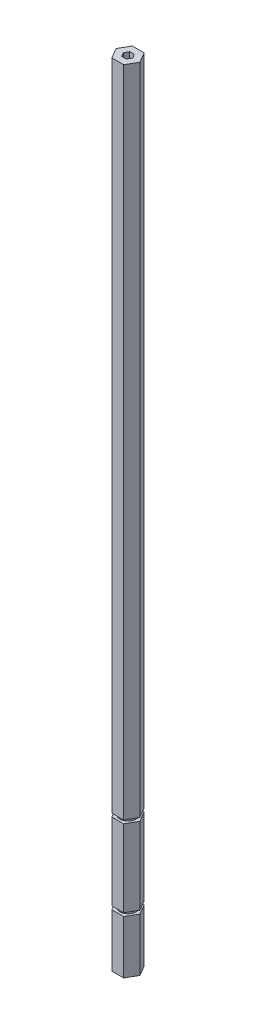
SolidWorks part; units mm, degrees
ref_plane "Front Plane" through (0, 0, 0) normal (0, 0, 1) x (1, 0, 0)
ref_plane "Top Plane" through (0, 0, 0) normal (0, 1, 0) x (1, 0, 0)
ref_plane "Right Plane" through (0, 0, 0) normal (1, 0, 0) x (0, 0, -1)
sketch "Sketch1" plane through (0, 0, 0) normal (0, 1, 0) x (1, 0, 0)
  line L9 (7.3323, 0) -> (3.6662, 6.35)
  line L10 (3.6662, 6.35) -> (-3.6662, 6.35)
  line L11 (-3.6662, 6.35) -> (-7.3323, 0)
  line L12 (-7.3323, 0) -> (-3.6662, -6.35)
  line L13 (-3.6662, -6.35) -> (3.6662, -6.35)
  line L14 (3.6662, -6.35) -> (7.3323, 0)
  line L15 (1.4434, 2.5) -> (-1.4434, 2.5)
  line L16 (-1.4434, 2.5) -> (-2.8868, 0)
  line L17 (-2.8868, 0) -> (-1.4434, -2.5)
  line L18 (-1.4434, -2.5) -> (1.4434, -2.5)
  line L19 (1.4434, -2.5) -> (2.8868, 0)
  line L20 (2.8868, 0) -> (1.4434, 2.5)
  circle A0 centre (0, 0) radius 6.35 construction
  circle A1 centre (0, 0) radius 2.5 construction
  dimension "D1" = 12.7
  dimension "D2" = 5
extrude "Boss-Extrude1" add sketch "Sketch1" along normal blind 488.95
sketch "Sketch3" plane through (0, 0, 0) normal (1, 0, 0) x (0, 0, -1)
  line L0 (0, 488.95) -> (0, 431.8613) construction
  line L2 (0, 488.95) -> (0, 0) construction
  line L7 (-5.0165, 84.582) -> (5.0165, 84.582) construction
  line L10 (5.0165, 84.582) -> (7.5565, 84.582)
  line L11 (5.0165, 84.582) -> (5.0165, 82.55)
  line L12 (5.0165, 82.55) -> (7.5565, 82.55)
  line L13 (7.5565, 84.582) -> (7.5565, 82.55)
  line L14 (0, 0) -> (6.35, 0) construction
  line L15 (5.0165, 82.55) -> (5.0165, 34.925) construction
  line L16 (5.0165, 58.7375) -> (-13.2923, 58.7375) construction
  line L17 (5.0165, 32.893) -> (7.5565, 32.893)
  line L18 (5.0165, 32.893) -> (5.0165, 34.925)
  line L19 (5.0165, 34.925) -> (7.5565, 34.925)
  line L20 (7.5565, 32.893) -> (7.5565, 34.925)
  point P7 (0, 84.582)
  dimension "D1" = 10.033
  dimension "D2" = 82.55
  dimension "D3" = 2.032
  dimension "D4" = 2.54
  dimension "D5" = 47.625
revolve "Cut-Revolve2" cut sketch "Sketch3" angle 360 about L0
